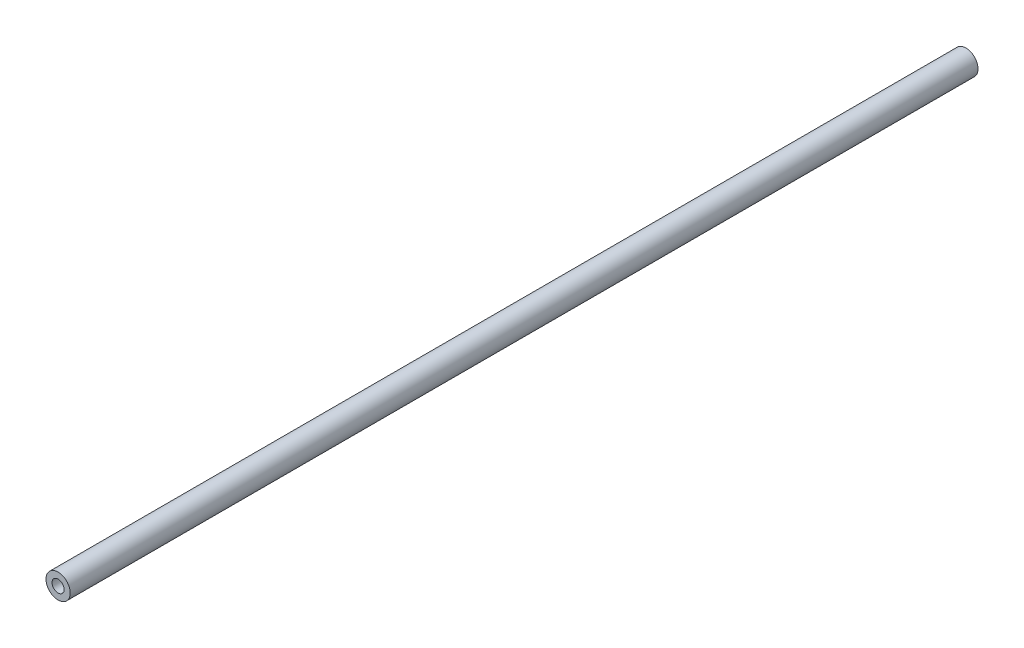
SolidWorks part; units mm, degrees
ref_plane "Plano frontal" through (0, 0, 0) normal (0, 0, 1) x (1, 0, 0)
ref_plane "Plano superior" through (0, 0, 0) normal (0, 1, 0) x (1, 0, 0)
ref_plane "Plano direito" through (0, 0, 0) normal (1, 0, 0) x (0, 0, -1)
sketch "Esboço1" plane through (0, 0, 0) normal (0, 1, 0) x (1, 0, 0)
  line L0 (0, 0) -> (0, 50000) construction
  line L1 (-2, 75) -> (-1, 75)
  line L2 (-2, 75) -> (-2, -75)
  line L3 (-2, -75) -> (-1, -75)
  line L4 (-1, 75) -> (-1, -75)
  point P8 (-2, 0)
  dimension "D1" = 150
  dimension "D2" = 1
  dimension "D3" = 2
revolve "Revolução1" add sketch "Esboço1" angle 360 about L0
